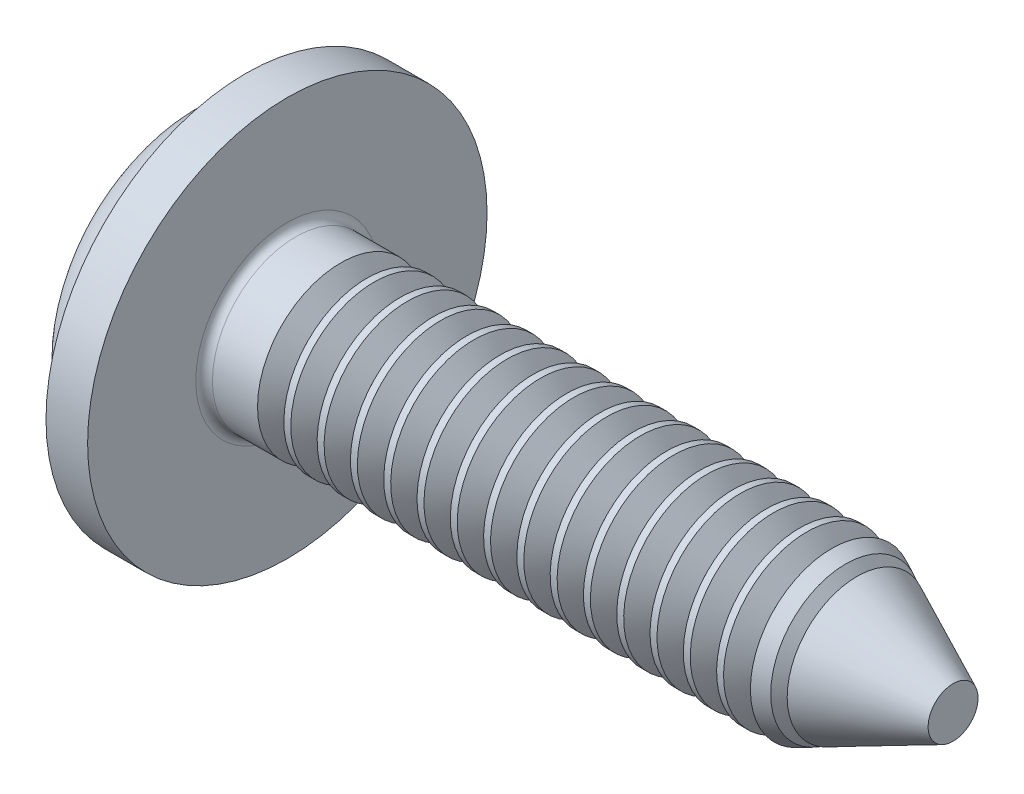
SolidWorks part; units mm, degrees
material "Aço NB 1045"
ref_plane "Plane1" through (0, 0, 0) normal (0, 0, 1) x (1, 0, 0)
ref_plane "Plane2" through (0, 0, 0) normal (0, 1, 0) x (1, 0, 0)
ref_plane "Plane3" through (0, 0, 0) normal (1, 0, 0) x (0, 0, -1)
sketch "BodySke" plane through (0, 0, 0) normal (0, 0, 1) x (1, 0, 0)
  line L0 (1.6, 1) -> (1.6, 2)
  line L1 (1.8, 6.35) -> (1.8, -3.175) construction
  line L2 (-25.4, 0) -> (127, 0) construction
  line L3 (9.6, 0) -> (0, 0)
  line L4 (1.6, 1) -> (9.6, 1)
  line L5 (9.6, 1) -> (9.6, 0)
  line L6 (1.1, 2) -> (1.6, 2)
  line L8 (1.6, 6.35) -> (1.6, -3.175) construction
  arc A0 (0.3941, 1.5765) -> (0, 0) centre (3.35, 0) ccw
  arc A2 (0.3941, 1.5765) -> (1.1, 2) centre (1.1, 1.2) cw
  dimension "D2" = 0.8
  dimension "Length" = 8
  dimension "Head_ht" = 1.6
  dimension "Head_dia" = 4
  dimension "Advance" = 0.4
  dimension "Thread_nom" = 8
  dimension "Diameter" = 2
  dimension "D1" = 0.5
revolve "Base-Revolve" add sketch "BodySke"
cosmetic thread "ThreadCosmetic" [suppressed]
fillet "Fillet1" radius 0.1 1 edges at (1.6, 0, 1)
sketch "Sketch3" plane through (0, 0, 0) normal (1, 0, 0) x (0, 0, -1)
  line L0 (0.24, -1.05) -> (-0.24, -1.05)
  line L1 (0.24, -1.05) -> (0.24, 1.05)
  line L2 (-0.24, 1.05) -> (0.24, 1.05)
  line L3 (-0.24, 1.05) -> (-0.24, -1.05)
  dimension "Cross_dia" = 2.1
  dimension "D1" = 1.05
  dimension "Cross_width" = 0.48
  dimension "D2" = 0.24
ref_plane "Plane4" through (1.42, 0, 0) normal (1, 0, 0) x (0, 0, -1)
sketch "Sketch4" plane through (1.42, 0, 0) normal (1, 0, 0) x (0, 0, -1)
  line L0 (0.24, -0.342) -> (-0.24, -0.342)
  line L1 (0.24, -0.342) -> (0.24, 0.342)
  line L2 (-0.24, 0.342) -> (0.24, 0.342)
  line L3 (-0.24, 0.342) -> (-0.24, -0.342)
  dimension "D1" = 0.48
  dimension "D2" = 0.684
  dimension "D3" = 0.24
  dimension "D4" = 0.342
loft "Recess" cut profiles "Sketch3", "Sketch4"
pattern_circular "RecPat" count 2 every 90 about axis through (0, 0, 0) along (1, 0, 0) of "Recess"
sketch "RecCorSke" plane through (0, 0, 0) normal (0, 0, 1) x (1, 0, 0)
  line L0 (-3.175, 0) -> (15.875, 0) construction
  line L1 (-25.4, 0) -> (127, 0) construction
  line L2 (0, 0) -> (0, 0.4548)
  line L3 (0, 0.4548) -> (1.42, 0.3555)
  line L4 (1.42, 0.3555) -> (1.5355, 0)
  line L5 (1.5355, 0) -> (0, 0)
  dimension "Diameter" = 0.711
  dimension "Depth" = 1.42
  dimension "Draft_angle" = 4
  dimension "Bottom_angle" = 18
revolve "RecessCore" cut sketch "RecCorSke" angle 360 about L0
sketch "ThdSchSke" plane through (0, 0, 0) normal (0, 0, 1) x (1, 0, 0)
  line L0 (2.4, -0.774) -> (2.2418, -1)
  line L1 (2.4, -0.774) -> (2.5582, -1)
  line L2 (2.5582, -1) -> (2.5582, -1.25)
  line L3 (-3.175, 0) -> (5.1513, 0) construction
  line L5 (2.5582, -1.25) -> (2.2418, -1.25)
  line L6 (2.2418, -1.25) -> (2.2418, -1)
  dimension "Diameter" = 2
  dimension "SideAngle" = 55
  dimension "VeeAngle" = 70
  dimension "Thread_minor" = 1.548
  dimension "Overcut" = 2.5
  dimension "Start" = 2.4
revolve "ThreadSchematic" cut sketch "ThdSchSke" angle 360 about L3
pattern_linear "ThdSchPat" count 19 spacing 0.4 along (1, 0, 0) of "ThreadSchematic"
sketch "Esboço1" plane through (1.6, 0, 0) normal (1, 0, 0) x (0, 0, -1)
  circle A0 centre (0, 0) radius 2.4
  dimension "D1" = 4.8
extrude "Ressalto-extrusão1" add sketch "Esboço1" against normal blind 0.5
sketch "Esboço2" plane through (0, 0, 0) normal (0, 1, 0) x (1, 0, 0)
  line L0 (0, 0) -> (9.6, 0) construction
  line L1 (9.6, -0.774) -> (9.6, 0.774) construction
  line L2 (9.6, 0.3) -> (8.1, 1)
  line L4 (8.1, 1) -> (9.6, 1)
  line L5 (9.6, 1) -> (9.6, 0.3)
  line L6 (7.4418, 1) -> (7.3582, 1) construction
  point P7 (7.6027, 1.1019)
  point P8 (7.4268, 1)
  point P9 (0, 0)
  dimension "D1" = 1.5
  dimension "D2" = 0.6
revolve "Corte-Revolução1" cut sketch "Esboço2" angle 360 about L0
equation "\"D1@Sketch3\" = \"Cross_dia@Sketch3\" / 2"
equation "\"D2@Sketch3\" = \"Cross_width@Sketch3\" / 2"
equation "\"Depth@RecCorSke\" = \"Cross_depth@Plane4\""
equation "\"D1@Sketch4\" = \"Cross_width@Sketch3\""
equation "\"D2@Sketch4\" = \"Cross_dia@Sketch3\" - 2.0 * \"Cross_depth@Plane4\" * tan(26.5  * 0.017453292)"
equation "\"D3@Sketch4\" = \"D1@Sketch4\" / 2"
equation "\"D4@Sketch4\" = \"D2@Sketch4\" / 2"
equation "\"Thread_length@ThreadCosmetic\" = ((sgn( (\"Length@BodySke\" - \"Advance@BodySke\" * 2.0 ) - \"Thread_nom@BodySke\" )-1)*( (\"Length@BodySke\" - \"Advance@BodySke\" * 2.0 ) - \"Thread_nom@BodySke\" ))/-2+ \"Thread_nom@BodySke\""
equation "\"Thread_minor@ThdSchSke\" = \"Thread_minor@ThreadCosmetic\""
equation "\"Diameter@ThdSchSke\" = \"Diameter@BodySke\""
equation "\"Overcut@ThdSchSke\" = \"Diameter@BodySke\" * 1.25"
equation "\"Start@ThdSchSke\" = \"Head_ht@BodySke\" + \"Length@BodySke\" - \"Thread_length@ThreadCosmetic\"  '---Non-countersunk---"
equation "\"Num_threads@ThdSchPat\" = int( \"Thread_length@ThreadCosmetic\" / \"Advance@BodySke\" + 0.999 )  + 1"
equation "\"Advance@ThdSchPat\" = \"Thread_length@ThreadCosmetic\" /  (\"Num_threads@ThdSchPat\" - 1) 'relax it"
